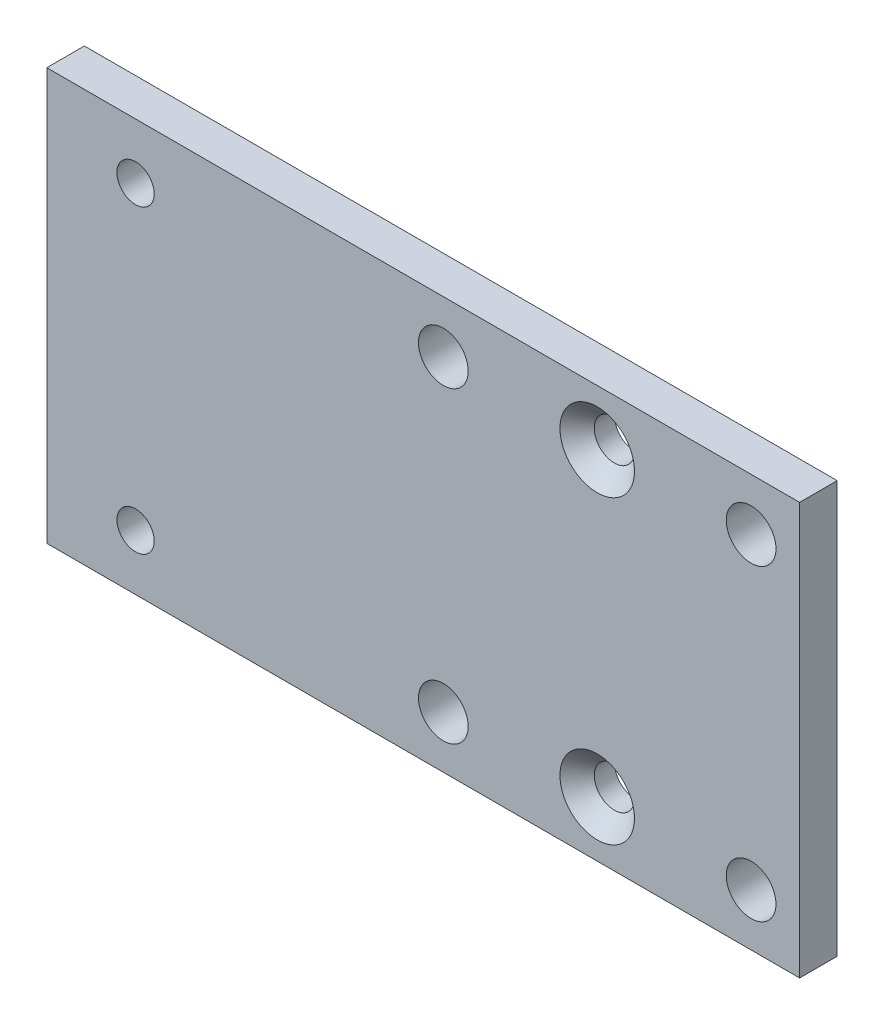
SolidWorks part; units mm, degrees
ref_plane "Top Plane" through (0, 0, 0) normal (0, 0, 1) x (1, 0, 0)
ref_plane "Front Plane" through (0, 0, 0) normal (0, 1, 0) x (1, 0, 0)
ref_plane "Right Plane" through (0, 0, 0) normal (1, 0, 0) x (0, 0, -1)
sketch "Profile Sketch" plane through (0, 0, 0) normal (0, 0, 1) x (1, 0, 0)
  line L1 (-31.8, -17.4) -> (31.8, -17.4)
  line L2 (-31.8, -17.4) -> (-31.8, 17.4)
  line L3 (-31.8, 17.4) -> (31.8, 17.4)
  line L4 (31.8, -17.4) -> (31.8, 17.4)
  line L5 (-31.8, -17.4) -> (31.8, 17.4) construction
  line L6 (-31.8, 17.4) -> (31.8, -17.4) construction
  point P0 (0, 0)
  dimension "D1" = 63.6
  dimension "D2" = 34.8
extrude "Profile Extrude" add sketch "Profile Sketch" along normal blind 3.175
sketch "Mounting Hole Sketch" plane through (0, 0, 3.175) normal (0, 0, 1) x (1, 0, 0)
  line L0 (31.8, 0) -> (-31.8, 0) construction
  line L1 (31.8, -17.4) -> (31.8, 17.4) construction
  line L2 (-31.8, 17.4) -> (-31.8, -17.4) construction
  circle A0 centre (-24.3, 12.7) radius 1.575
  circle A3 centre (-24.3, -12.7) radius 1.575
  point P0 (-24.3, 12.7)
  point P1 (14.7, 12.7)
  point P2 (-24.3, -12.7)
  point P3 (14.7, -12.7)
  dimension "D2" = 3.15
  dimension "D4" = 3.15
  dimension "D1" = 7.5
  dimension "D6" = 25.4
  dimension "D7" = 39
extrude "Mounting Hole Cut" cut sketch "Mounting Hole Sketch" against normal through all
sketch "Inset Screw Sketch" plane through (0, 0, 3.175) normal (0, 0, 1) x (1, 0, 0)
  circle A0 centre (-24.3, 12.7) radius 1.575 construction
  point P0 (14.7, 12.7)
  point P1 (14.7, -12.7)
  point P4 (-24.3, 12.7)
  point P5 (-24.3, -12.7)
  dimension "D1" = 39
hole_wizard "CSK for M3 Flat Head Machine Screw1" positions "3DSketch1" profile "Sketch2" countersink size "M3" standard "ANSI Metric" end condition through all
sketch3d "3DSketch1"
  point P0 (14.7, 12.7, 3.175)
  point P3 (14.7, -12.7, 3.175)
sketch "Sketch2" plane through (14.7, 12.7, 3.175) normal (1, 0, 0) x (0, -1, 0)
  line L0 (0, 0) -> (0, 3.175)
  line L1 (0, 3.175) -> (1.7, 3.175)
  line L2 (1.7, 3.175) -> (1.7, 1.45)
  line L3 (1.7, 1.45) -> (3.15, 0)
  line L5 (3.15, 0) -> (0, 0)
  line L6 (-1.7, 1.45) -> (-3.15, 0) construction
  line L11 (0, -6.35) -> (0, 107.95) construction
  dimension "Thru Hole Dia." = 3.4
  dimension "Thru Hole Depth" = 3.175
  dimension "Near C'Sink Dia." = 6.3
  dimension "Near C'Sink Angle" = 90
sketch "Carriage Guide Hole Sketch" plane through (0, 0, 3.175) normal (0, 0, 1) x (1, 0, 0)
  line L0 (-31.8, 0) -> (31.8, 0) construction
  line L1 (-31.8, 17.4) -> (-31.8, -17.4) construction
  line L2 (31.8, -17.4) -> (31.8, 17.4) construction
  line L3 (14.7, 12.7) -> (14.7, -12.7) construction
  line L4 (1.7, 13) -> (27.7, 13) construction
  circle A0 centre (1.7, 13) radius 2.1
  circle A1 centre (27.7, 13) radius 2.1
  circle A2 centre (27.7, -13) radius 2.1
  circle A3 centre (1.7, -13) radius 2.1
  point P18 (14.7, 13)
  dimension "D1" = 4.2
  dimension "D2" = 4.2
  dimension "D3" = 4.2
  dimension "D4" = 4.2
  dimension "D5" = 26
  dimension "D6" = 26
extrude "Carriage Guide Hole Cut" cut sketch "Carriage Guide Hole Sketch" against normal through all
equation "\"D2@Carriage Guide Hole Sketch\"=\"D1@Carriage Guide Hole Sketch\""
equation "\"D3@Carriage Guide Hole Sketch\"=\"D1@Carriage Guide Hole Sketch\""
equation "\"D4@Carriage Guide Hole Sketch\"=\"D1@Carriage Guide Hole Sketch\""
equation "\"D4@Mounting Hole Sketch\"=\"D2@Mounting Hole Sketch\""
